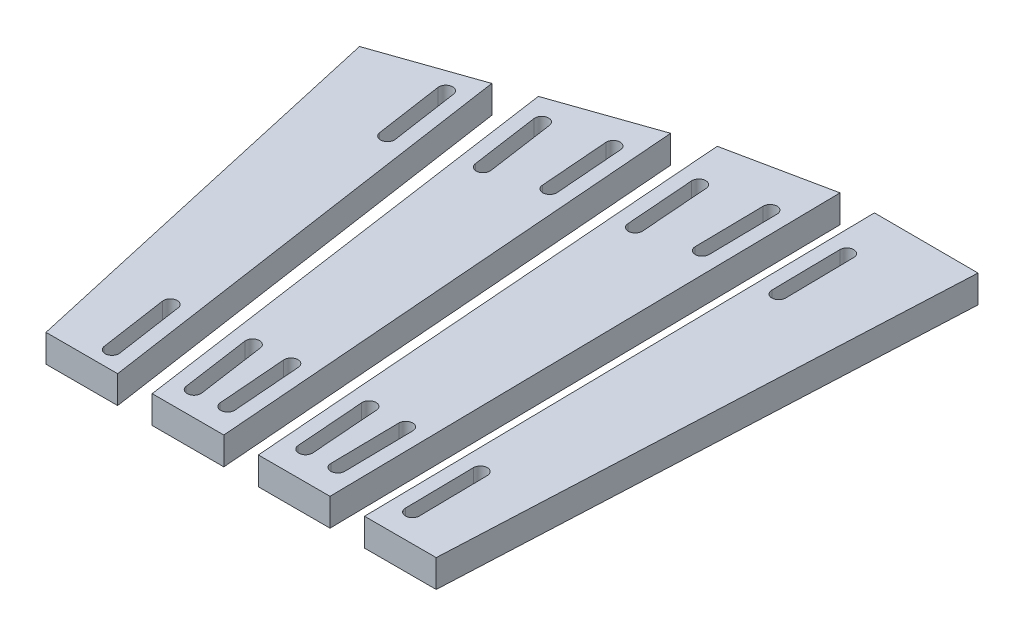
SolidWorks part; units mm, degrees
ref_plane "Front Plane" through (0, 0, 0) normal (0, 0, 1) x (1, 0, 0)
ref_plane "Top Plane" through (0, 0, 0) normal (0, 1, 0) x (1, 0, 0)
ref_plane "Right Plane" through (0, 0, 0) normal (1, 0, 0) x (0, 0, -1)
sketch "Sketch2" plane through (0, 0, 0) normal (0, 1, 0) x (1, 0, 0)
  line L0 (-34.0674, -37.5) -> (22.4357, -37.5) construction
  line L1 (22.4357, -37.5) -> (25.977, 37.4163) construction
  line L2 (25.977, 37.4163) -> (0, 37.5) construction
  line L3 (0, 37.5) -> (-47.2137, 21.0421) construction
  line L4 (-47.2137, 21.0421) -> (-34.0674, -37.5) construction
  dimension "D1" = 60
  dimension "D2" = 75
  dimension "D3" = 75
  dimension "D4" = 37.5
  dimension "D5" = 75
  dimension "D6" = 50
  dimension "D7" = 25.977
  dimension "D8" = 0
sketch "Sketch3" plane through (0, 0, 0) normal (0, 1, 0) x (1, 0, 0)
  line L0 (-47.2137, 21.0421) -> (-33.0072, 25.9942)
  line L1 (-28.0072, 27.7371) -> (-13.8006, 32.6893)
  line L2 (22.4357, -37.5) -> (12.0599, -37.5)
  line L3 (-8.8006, 34.4322) -> (5.9322, 37.4809)
  line L4 (10.9322, 37.4648) -> (25.977, 37.4163)
  line L5 (25.977, 37.4163) -> (0, 37.5) construction
  line L6 (7.0599, -37.5) -> (-3.3158, -37.5)
  line L7 (0, 37.5) -> (-47.2137, 21.0421) construction
  line L8 (-47.2137, 21.0421) -> (-34.0674, -37.5)
  line L9 (-33.0072, 25.9942) -> (-23.6916, -37.5)
  line L10 (-18.6916, -37.5) -> (-8.3158, -37.5)
  line L12 (-28.0072, 27.7371) -> (-18.6916, -37.5)
  line L13 (-13.8006, 32.6893) -> (-8.3158, -37.5)
  line L14 (-23.6916, -37.5) -> (-34.0674, -37.5)
  line L15 (-8.8006, 34.4322) -> (-3.3158, -37.5)
  line L16 (5.9322, 37.4809) -> (7.0599, -37.5)
  line L17 (10.9322, 37.4648) -> (12.0599, -37.5)
  line L18 (25.977, 37.4163) -> (22.4357, -37.5)
  dimension "D1" = 5
  dimension "D2" = 5
  dimension "D3" = 5
  dimension "D4" = 5
  dimension "D5" = 5
  dimension "D6" = 5
extrude "Boss-Extrude1" add sketch "Sketch3" along normal blind 4
sketch "Sketch4" plane through (0, 0, 0) normal (0, 1, 0) x (1, 0, 0)
  line L0 (-34.4246, 21.8773) -> (-32.973, 11.9832)
  line L1 (-34.9518, 11.6929) -> (-36.4034, 21.587)
  line L2 (-27.5673, -24.8616) -> (-26.1156, -34.7557)
  line L3 (-28.0945, -35.046) -> (-29.5461, -25.1519)
  line L4 (-23.5634, 24.9137) -> (-22.1498, 15.0141)
  line L5 (-24.1297, 14.7314) -> (-25.5433, 24.6309)
  line L6 (-16.5883, -23.9333) -> (-15.1747, -33.8329)
  line L7 (-17.1546, -34.1156) -> (-18.5682, -24.216)
  line L8 (-15.363, 27.0108) -> (-14.584, 17.0412)
  line L9 (-16.5779, 16.8854) -> (-17.3569, 26.855)
  line L10 (-11.4081, -23.6006) -> (-10.629, -33.5703)
  line L11 (-12.6229, -33.7261) -> (-13.402, -23.7565)
  line L12 (-4.3268, 28.3699) -> (-3.5665, 18.3988)
  line L13 (-5.5607, 18.2468) -> (-6.321, 28.2178)
  line L14 (4.0403, 30.2743) -> (4.1907, 20.2743)
  line L15 (2.1909, 20.2443) -> (2.0405, 30.2443)
  line L16 (-0.3858, -23.3153) -> (0.3745, -33.2864)
  line L17 (-1.6197, -33.4384) -> (-2.38, -23.4674)
  line L18 (4.8461, -23.298) -> (4.9965, -33.298)
  line L19 (2.9967, -33.3281) -> (2.8463, -23.3281)
  line L20 (15.0394, 30.3686) -> (15.1898, 20.3686)
  line L21 (13.19, 20.3386) -> (13.0396, 30.3386)
  line L22 (15.8497, -23.4971) -> (16.0001, -33.4971)
  line L23 (14.0004, -33.5272) -> (13.8499, -23.5272)
  line L24 (-23.6916, -37.5) -> (-33.0072, 25.9942) construction
  line L25 (-28.0072, 27.7371) -> (-18.6916, -37.5) construction
  line L26 (-8.3158, -37.5) -> (-13.8006, 32.6893) construction
  line L27 (-8.8006, 34.4322) -> (-3.3158, -37.5) construction
  line L28 (7.0599, -37.5) -> (5.9322, 37.4809) construction
  line L29 (10.9322, 37.4648) -> (12.0599, -37.5) construction
  arc A0 (-32.973, 11.9832) -> (-34.9518, 11.6929) centre (-33.9624, 11.838) cw
  arc A1 (-36.4034, 21.587) -> (-34.4246, 21.8773) centre (-35.414, 21.7321) cw
  arc A2 (-26.1156, -34.7557) -> (-28.0945, -35.046) centre (-27.1051, -34.9008) cw
  arc A3 (-29.5461, -25.1519) -> (-27.5673, -24.8616) centre (-28.5567, -25.0067) cw
  arc A4 (-22.1498, 15.0141) -> (-24.1297, 14.7314) centre (-23.1398, 14.8727) cw
  arc A5 (-25.5433, 24.6309) -> (-23.5634, 24.9137) centre (-24.5534, 24.7723) cw
  arc A6 (-15.1747, -33.8329) -> (-17.1546, -34.1156) centre (-16.1646, -33.9742) cw
  arc A7 (-18.5682, -24.216) -> (-16.5883, -23.9333) centre (-17.5783, -24.0746) cw
  arc A8 (-14.584, 17.0412) -> (-16.5779, 16.8854) centre (-15.5809, 16.9633) cw
  arc A9 (-17.3569, 26.855) -> (-15.363, 27.0108) centre (-16.36, 26.9329) cw
  arc A10 (-10.629, -33.5703) -> (-12.6229, -33.7261) centre (-11.626, -33.6482) cw
  arc A11 (-13.402, -23.7565) -> (-11.4081, -23.6006) centre (-12.405, -23.6786) cw
  arc A12 (-3.5665, 18.3988) -> (-5.5607, 18.2468) centre (-4.5636, 18.3228) cw
  arc A13 (-6.321, 28.2178) -> (-4.3268, 28.3699) centre (-5.3239, 28.2939) cw
  arc A14 (4.1907, 20.2743) -> (2.1909, 20.2443) centre (3.1908, 20.2593) cw
  arc A15 (2.0405, 30.2443) -> (4.0403, 30.2743) centre (3.0404, 30.2593) cw
  arc A16 (0.3745, -33.2864) -> (-1.6197, -33.4384) centre (-0.6226, -33.3624) cw
  arc A17 (-2.38, -23.4674) -> (-0.3858, -23.3153) centre (-1.3829, -23.3913) cw
  arc A18 (4.9965, -33.298) -> (2.9967, -33.3281) centre (3.9966, -33.313) cw
  arc A19 (2.8463, -23.3281) -> (4.8461, -23.298) centre (3.8462, -23.313) cw
  arc A20 (15.1898, 20.3686) -> (13.19, 20.3386) centre (14.1899, 20.3536) cw
  arc A21 (13.0396, 30.3386) -> (15.0394, 30.3686) centre (14.0395, 30.3536) cw
  arc A22 (16.0001, -33.4971) -> (14.0004, -33.5272) centre (15.0003, -33.5122) cw
  arc A23 (13.8499, -23.5272) -> (15.8497, -23.4971) centre (14.8498, -23.5122) cw
  dimension "D1" = 10
  dimension "D2" = 2
  dimension "D3" = 2
  dimension "D4" = 2
  dimension "D5" = 2
  dimension "D6" = 2
  dimension "D7" = 2
  dimension "D8" = 2
  dimension "D9" = 2
  dimension "D10" = 2
  dimension "D11" = 2
  dimension "D12" = 2
  dimension "D13" = 2
  dimension "D14" = 10
  dimension "D15" = 10
  dimension "D16" = 10
  dimension "D17" = 10
  dimension "D18" = 10
  dimension "D19" = 10
  dimension "D20" = 10
  dimension "D21" = 10
  dimension "D22" = 10
  dimension "D23" = 10
  dimension "D24" = 10
  dimension "D25" = 2
  dimension "D26" = 2
  dimension "D27" = 2
  dimension "D28" = 2
  dimension "D29" = 2
  dimension "D30" = 2
  dimension "D31" = 2
  dimension "D32" = 2
  dimension "D33" = 2
  dimension "D34" = 2
  dimension "D35" = 2
  dimension "D36" = 2
extrude "Cut-Extrude1" cut sketch "Sketch4" along normal through all
equation "\"D4@Sketch2\" = \"D3@Sketch2\" / 2"
equation "\"D2@Sketch3\"=\"D1@Sketch3\""
equation "\"D3@Sketch3\"=\"D1@Sketch3\""
equation "\"D5@Sketch3\"=\"D1@Sketch3\""
equation "\"D6@Sketch3\"=\"D1@Sketch3\""
equation "\"D4@Sketch3\" = \"D1@Sketch3\""
equation "\"slot_width\"= 2mm"
equation "\"slot_length\"= 10mm"
equation "\"D2@Sketch4\"=\"slot_width\""
equation "\"D1@Sketch4\"=\"slot_length\""
equation "\"D3@Sketch4\"=\"slot_width\""
equation "\"D4@Sketch4\"=\"slot_width\""
equation "\"D5@Sketch4\"=\"slot_width\""
equation "\"D6@Sketch4\"=\"slot_width\""
equation "\"D7@Sketch4\"=\"slot_width\""
equation "\"D8@Sketch4\"=\"slot_width\""
equation "\"D10@Sketch4\"=\"slot_width\""
equation "\"D11@Sketch4\"=\"slot_width\""
equation "\"D12@Sketch4\"=\"slot_width\""
equation "\"D13@Sketch4\"=\"slot_width\""
equation "\"D9@Sketch4\"=\"slot_width\""
equation "\"D14@Sketch4\"=\"slot_length\""
equation "\"D15@Sketch4\"=\"slot_length\""
equation "\"D16@Sketch4\"=\"slot_length\""
equation "\"D17@Sketch4\"=\"slot_length\""
equation "\"D18@Sketch4\"=\"slot_length\""
equation "\"D19@Sketch4\"=\"slot_length\""
equation "\"D20@Sketch4\"=\"slot_length\""
equation "\"D21@Sketch4\"=\"slot_length\""
equation "\"D22@Sketch4\"=\"slot_length\""
equation "\"D23@Sketch4\"=\"slot_length\""
equation "\"D24@Sketch4\"=\"slot_length\""
equation "\"slot_distance\"= 2mm"
equation "\"D25@Sketch4\"=\"slot_distance\""
equation "\"D26@Sketch4\"=\"slot_distance\""
equation "\"D27@Sketch4\"=\"slot_distance\""
equation "\"D28@Sketch4\"=\"slot_distance\""
equation "\"D29@Sketch4\"=\"slot_distance\""
equation "\"D30@Sketch4\"=\"slot_distance\""
equation "\"D31@Sketch4\"=\"slot_distance\""
equation "\"D32@Sketch4\"=\"slot_distance\""
equation "\"D33@Sketch4\"=\"slot_distance\""
equation "\"D34@Sketch4\"=\"slot_distance\""
equation "\"D35@Sketch4\"=\"slot_distance\""
equation "\"D36@Sketch4\"=\"slot_distance\""
